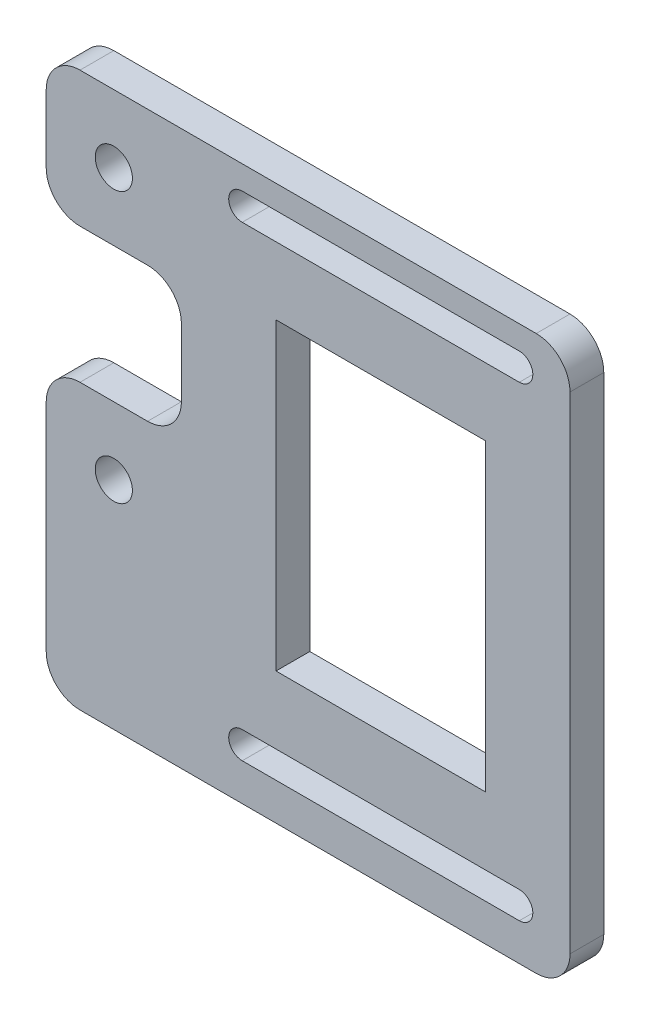
SolidWorks part; units mm, degrees
ref_plane "Front Plane" through (0, 0, 0) normal (0, 0, 1) x (1, 0, 0)
ref_plane "Top Plane" through (0, 0, 0) normal (0, 1, 0) x (1, 0, 0)
ref_plane "Right Plane" through (0, 0, 0) normal (1, 0, 0) x (0, 0, -1)
sketch "Sketch2" plane through (0, 0, 0) normal (0, 0, 1) x (1, 0, 0)
  line L0 (0, 20) -> (0, -20) construction
  line L1 (-10, 30) -> (-10, 10)
  line L2 (-10, 10) -> (10, 10)
  line L3 (10, 10) -> (10, -10)
  line L4 (10, -10) -> (-10, -10)
  line L5 (-10, -10) -> (-10, -52)
  line L6 (-10, -52) -> (67.5, -52)
  line L7 (67.5, -52) -> (67.5, 30)
  line L8 (67.5, 30) -> (-10, 30)
  line L9 (19, 24.5) -> (60, 24.5) construction
  line L10 (19, 26.5) -> (60, 26.5)
  line L11 (19, 22.5) -> (60, 22.5)
  line L12 (19, -44.5) -> (60, -44.5) construction
  line L13 (19, -42.5) -> (60, -42.5)
  line L14 (19, -46.5) -> (60, -46.5)
  line L15 (60, 24.5) -> (60, -44.5) construction
  line L16 (24, 12.5) -> (55, 12.5)
  line L17 (24, 12.5) -> (24, -32.5)
  line L18 (24, -32.5) -> (55, -32.5)
  line L19 (55, 12.5) -> (55, -32.5)
  arc A0 (19, 26.5) -> (19, 22.5) centre (19, 24.5) ccw
  arc A1 (60, 22.5) -> (60, 26.5) centre (60, 24.5) ccw
  arc A2 (19, -42.5) -> (19, -46.5) centre (19, -44.5) ccw
  arc A3 (60, -46.5) -> (60, -42.5) centre (60, -44.5) ccw
  point P0 (0, 20)
  point P1 (0, -20)
  point P5 (35, -20)
  point P16 (39.5, 24.5)
  point P21 (39.5, -44.5)
  point P32 (10, 0)
  point P33 (24, -10)
  point P36 (60, -10)
  point P37 (39.5, 12.5)
  point P38 (0, 10)
  point P39 (-10, 20)
  dimension "D4" = 2
  dimension "D1" = 40
  dimension "D2" = 35
  dimension "D3" = 10
  dimension "D5" = 7.5
  dimension "D6" = 45
  dimension "D7" = 31
  dimension "D8" = 11
  dimension "D9" = 7.5
  dimension "D10" = 12.5
  dimension "D11" = 10
  dimension "D12" = 5
  dimension "D13" = 10
  dimension "D14" = 69
  dimension "D15" = 24.5
extrude "Boss-Extrude1" add sketch "Sketch2" along normal blind 5
hole_wizard "M5 Clearance Hole1" positions "Sketch4" profile "Sketch3" hole size "M5" standard "ANSI Metric" end condition through all
sketch "Sketch4" plane through (0, 0, 5) normal (0, 0, 1) x (1, 0, 0)
  point P1 (0, 20)
  point P3 (0, -20)
sketch "Sketch3" plane through (0, 20, 5) normal (1, 0, 0) x (0, -1, 0)
  line L0 (0, 0) -> (0, 5)
  line L1 (0, 5) -> (2.75, 5)
  line L2 (2.75, 5) -> (2.75, 0)
  line L5 (2.75, 0) -> (0, 0)
  line L11 (0, -6.35) -> (0, 107.95) construction
  dimension "Thru Hole Dia." = 5.5
  dimension "Thru Hole Depth" = 5
fillet "Fillet1" radius 5 8 edges at (67.5, 30, 2.5) (67.5, -52, 2.5) (-10, -52, 2.5) (-10, -10, 2.5) (10, -10, 2.5) (10, 10, 2.5) (-10, 10, 2.5) (-10, 30, 2.5)
sketch "Sketch5" plane through (0, 0, 5) normal (0, 0, 1) x (1, 0, 0)
  circle A0 centre (0, -20) radius 7.5
  circle A1 centre (0, 20) radius 7.5
  circle A2 centre (0, 20) radius 2.75 construction
  circle A3 centre (0, -20) radius 2.75 construction
  circle A4 centre (0, 20) radius 2.75
  circle A5 centre (0, -20) radius 2.75
  dimension "D1" = 15
extrude "Boss-Extrude2" [suppressed] add sketch "Sketch5" along normal blind 5
equation "\"d_gearaxes\"= 40mm"
equation "\"d_servoaxis\"= 35mm"
equation "\"d1_servospacing\"= 30mm"
equation "\"d2_servospacing\"= 45mm"
equation "\"D1@Sketch2\"=\"d_gearaxes\""
equation "\"D2@Sketch2\"=\"d_servoaxis\""
